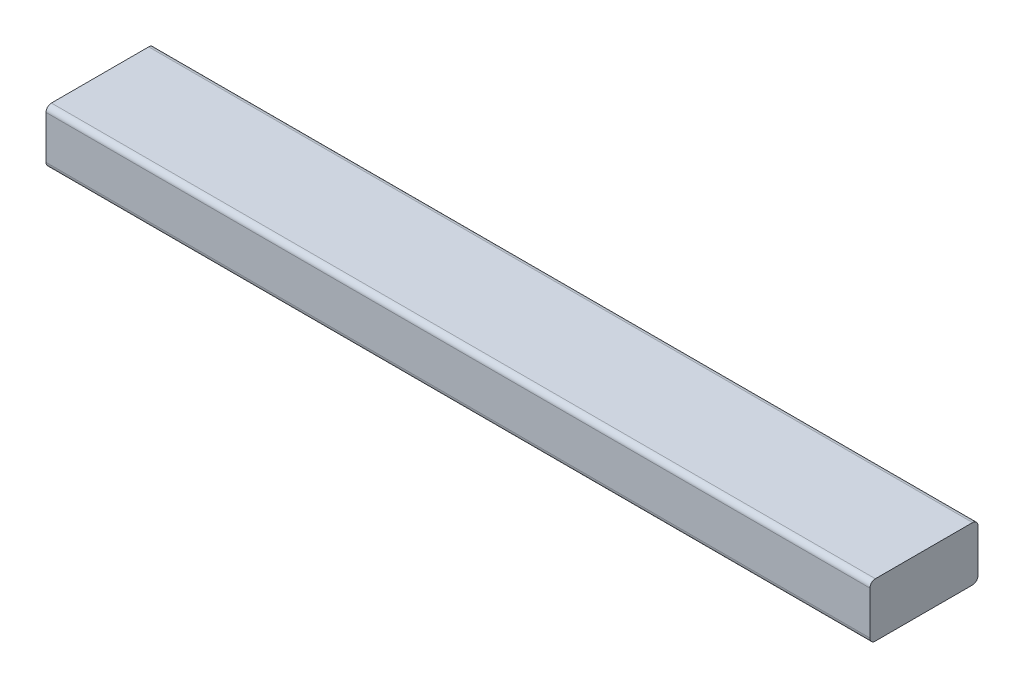
SolidWorks part; units mm, degrees
material "Balsa"
ref_plane "Front Plane" through (0, 0, 0) normal (0, 0, 1) x (1, 0, 0)
ref_plane "Top Plane" through (0, 0, 0) normal (0, 1, 0) x (1, 0, 0)
ref_plane "Right Plane" through (0, 0, 0) normal (1, 0, 0) x (0, 0, -1)
sketch "Sketch1" plane through (0, -12.7, 0) normal (0, -1, 0) x (-1, 0, 0)
  line L0 (-2587.3, -275) -> (-2587.3, 275) construction
  line L1 (-2587.3, -160.7) -> (-1812.7, -160.7)
  line L2 (-2587.3, -160.7) -> (-2587.3, -262.3)
  line L3 (-2587.3, -262.3) -> (-1812.7, -262.3)
  line L4 (-1812.7, -160.7) -> (-1812.7, -262.3)
  line L5 (-1812.7, 275) -> (-1812.7, -275) construction
  line L6 (-1812.7, -262.3) -> (-2587.3, -262.3) construction
  dimension "D1" = 101.6
extrude "Boss-Extrude1" add sketch "Sketch1" against normal blind 50.8
fillet "Fillet1" radius 5.08 4 edges at (2200, 38.1, 262.3) (2200, -12.7, 262.3) (2200, 38.1, 160.7) (2200, -12.7, 160.7)
